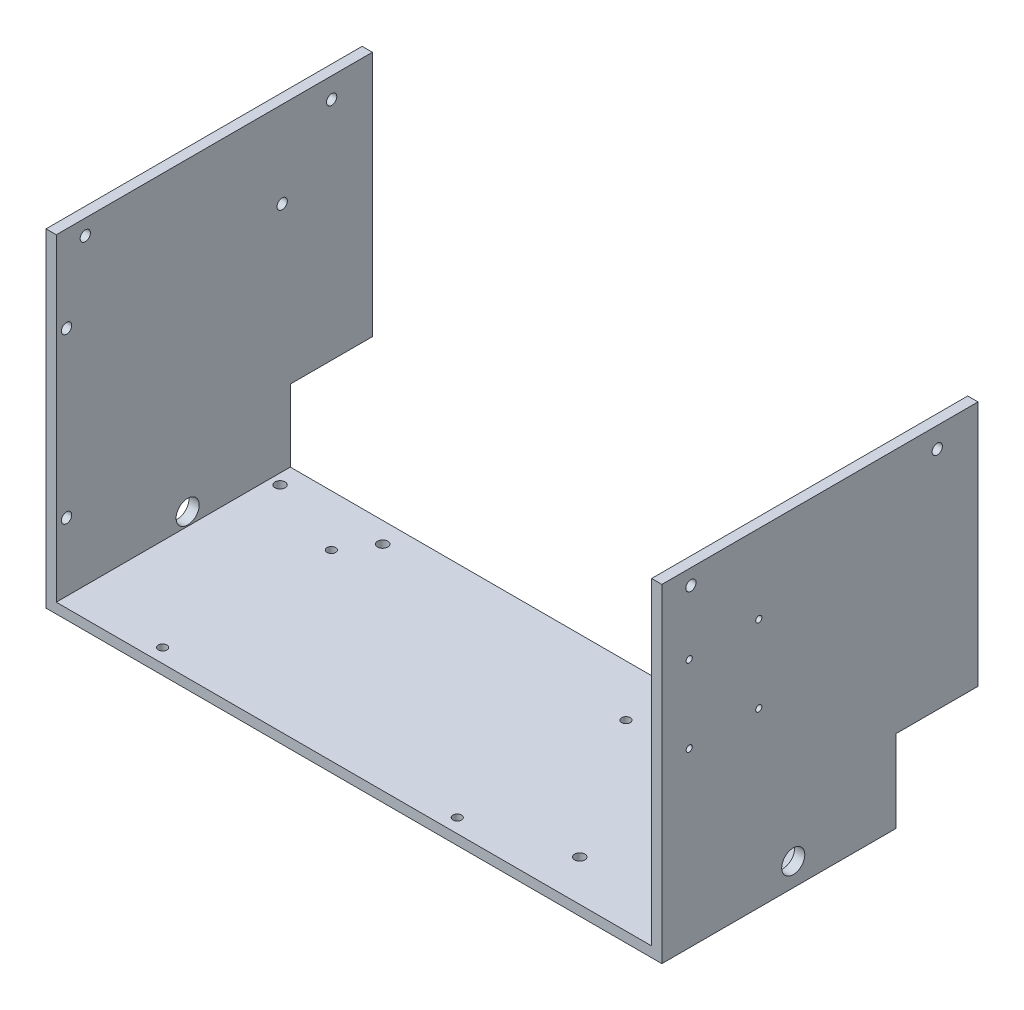
SolidWorks part; units mm, degrees
ref_plane "Front Plane" through (0, 0, 0) normal (0, 0, 1) x (1, 0, 0)
ref_plane "Top Plane" through (0, 0, 0) normal (0, 1, 0) x (1, 0, 0)
ref_plane "Right Plane" through (0, 0, 0) normal (1, 0, 0) x (0, 0, -1)
sketch "Sketch1" plane through (0, 0, 0) normal (0, 1, 0) x (1, 0, 0)
  line L1 (0, 0) -> (381, 0)
  line L2 (0, 0) -> (0, 429.26)
  line L3 (0, 429.26) -> (381, 429.26)
  line L4 (381, 0) -> (381, 429.26)
  dimension "D1" = 429.26
  dimension "D2" = 381
extrude "Boss-Extrude1" add sketch "Sketch1" along normal blind 6.35
sketch "Sketch2" plane through (0, 6.35, 0) normal (0, 1, 0) x (1, 0, 0)
  line L0 (0, 0) -> (381, 0) construction
  line L1 (63.5, 203.2) -> (317.5, 203.2)
  line L2 (63.5, 203.2) -> (63.5, 0)
  line L3 (63.5, 0) -> (317.5, 0)
  line L4 (317.5, 203.2) -> (317.5, 0)
  line L5 (381, 0) -> (381, 429.26) construction
  dimension "D1" = 254
  dimension "D2" = 203.2
  dimension "D3" = 0
  dimension "D4" = 63.5
extrude "Cut-Extrude1" cut sketch "Sketch2" against normal blind 6.35
sketch "Sketch3" plane through (0, 6.35, 0) normal (0, 1, 0) x (1, 0, 0)
  line L0 (381, 0) -> (381, 429.26) construction
  line L1 (0, 0) -> (381, 0)
  line L2 (0, 0) -> (0, 73.66)
  line L3 (0, 73.66) -> (381, 73.66)
  line L4 (381, 0) -> (381, 73.66)
  dimension "D1" = 73.66
extrude "Cut-Extrude2" cut sketch "Sketch3" against normal blind 6.35
sketch "Sketch4" plane through (0, 0, -203.2) normal (0, 0, 1) x (1, 0, 0)
  line L0 (317.5, 6.35) -> (63.5, 6.35) construction
  line L1 (63.5, 0) -> (317.5, 0)
  line L2 (63.5, 0) -> (63.5, 6.35)
  line L3 (63.5, 6.35) -> (317.5, 6.35)
  line L4 (317.5, 0) -> (317.5, 6.35)
  line L5 (63.5, 0) -> (63.5, 6.35) construction
  line L6 (317.5, 0) -> (63.5, 0) construction
  dimension "D1" = 254
  dimension "D2" = 0
  dimension "D3" = 0
extrude "Cut-Extrude3" cut sketch "Sketch4" against normal blind 73.66
sketch "Sketch6" plane through (0, 6.35, 0) normal (0, 1, 0) x (1, 0, 0)
  line L1 (381, 429.26) -> (374.65, 429.26)
  line L2 (381, 429.26) -> (381, 233.68)
  line L3 (381, 233.68) -> (374.65, 233.68)
  line L4 (374.65, 429.26) -> (374.65, 233.68)
  dimension "D1" = 6.35
  dimension "D2" = 195.58
extrude "Boss-Extrude2" add sketch "Sketch6" along normal blind 171.45
sketch "Sketch7" plane through (0, 6.35, 0) normal (0, 1, 0) x (1, 0, 0)
  line L1 (0, 429.26) -> (6.35, 429.26)
  line L2 (0, 429.26) -> (0, 233.68)
  line L3 (0, 233.68) -> (6.35, 233.68)
  line L4 (6.35, 429.26) -> (6.35, 233.68)
  dimension "D1" = 195.58
  dimension "D2" = 6.35
extrude "Boss-Extrude3" add sketch "Sketch7" along normal blind 158.75
sketch "Sketch8" plane through (0, 0, -429.26) normal (0, 0, -1) x (-1, 0, 0)
  line L1 (-6.35, 165.1) -> (0, 165.1)
  line L2 (-6.35, 165.1) -> (-6.35, 0)
  line L3 (-6.35, 0) -> (0, 0)
  line L4 (0, 165.1) -> (0, 0)
extrude "Boss-Extrude4" add sketch "Sketch8" along normal blind 50.8
sketch "Sketch9" plane through (0, 0, -233.68) normal (0, 0, 1) x (1, 0, 0)
  line L1 (6.35, 165.1) -> (0, 165.1)
  line L2 (6.35, 165.1) -> (6.35, 6.35)
  line L3 (6.35, 6.35) -> (0, 6.35)
  line L4 (0, 165.1) -> (0, 6.35)
extrude "Cut-Extrude4" cut sketch "Sketch9" against normal blind 50.8
sketch "Sketch10" plane through (0, 0, -429.26) normal (0, 0, -1) x (-1, 0, 0)
  line L0 (-381, 0) -> (-6.35, 0) construction
  line L1 (-381, 177.8) -> (-374.1001, 177.8)
  line L2 (-381, 177.8) -> (-381, 0)
  line L3 (-381, 0) -> (-374.1001, 0)
  line L4 (-374.1001, 177.8) -> (-374.1001, 0)
extrude "Boss-Extrude5" add sketch "Sketch10" along normal blind 50.8
sketch "Sketch11" plane through (0, 0, -233.68) normal (0, 0, 1) x (1, 0, 0)
  line L1 (381, 6.35) -> (374.65, 6.35)
  line L2 (381, 6.35) -> (381, 177.8)
  line L3 (381, 177.8) -> (374.65, 177.8)
  line L4 (374.65, 6.35) -> (374.65, 177.8)
extrude "Cut-Extrude5" cut sketch "Sketch11" against normal blind 50.8
sketch "Sketch13" plane through (0, 0, -429.26) normal (0, 0, 1) x (1, 0, 0)
  line L1 (374.65, 177.8) -> (374.1001, 177.8)
  line L2 (374.65, 177.8) -> (374.65, 6.35)
  line L3 (374.65, 6.35) -> (374.1001, 6.35)
  line L4 (374.1001, 177.8) -> (374.1001, 6.35)
extrude "Cut-Extrude6" cut sketch "Sketch13" against normal blind 50.8
sketch "Sketch14" plane through (0, 0, -480.06) normal (0, 0, -1) x (-1, 0, 0)
  line L1 (-381, 177.8) -> (-374.1001, 177.8)
  line L2 (-381, 177.8) -> (-381, 0)
  line L3 (-381, 0) -> (-374.1001, 0)
  line L4 (-374.1001, 177.8) -> (-374.1001, 0)
extrude "Cut-Extrude7" cut sketch "Sketch14" against normal blind 50.8
sketch "Sketch15" plane through (0, 0, -480.06) normal (0, 0, -1) x (-1, 0, 0)
  line L1 (-6.35, 165.1) -> (0, 165.1)
  line L2 (-6.35, 165.1) -> (-6.35, 0)
  line L3 (-6.35, 0) -> (0, 0)
  line L4 (0, 165.1) -> (0, 0)
extrude "Cut-Extrude8" cut sketch "Sketch15" against normal blind 50.8
sketch "Sketch16" plane through (0, 177.8, 0) normal (0, 1, 0) x (1, 0, 0)
  line L1 (381, 284.48) -> (374.65, 284.48)
  line L2 (381, 284.48) -> (381, 429.26)
  line L3 (381, 429.26) -> (374.65, 429.26)
  line L4 (374.65, 284.48) -> (374.65, 429.26)
extrude "Boss-Extrude6" add sketch "Sketch16" along normal blind 25.4
sketch "Sketch17" plane through (0, 165.1, 0) normal (0, 1, 0) x (1, 0, 0)
  line L1 (6.35, 284.48) -> (0, 284.48)
  line L2 (6.35, 284.48) -> (6.35, 429.26)
  line L3 (6.35, 429.26) -> (0, 429.26)
  line L4 (0, 284.48) -> (0, 429.26)
extrude "Boss-Extrude7" add sketch "Sketch17" against normal blind 19.05
sketch "Sketch19" plane through (0, 0, -429.26) normal (0, 0, -1) x (-1, 0, 0)
  line L0 (0, 0) -> (0, 165.1) construction
  line L1 (-6.35, 190.5) -> (0, 190.5)
  line L2 (-6.35, 190.5) -> (-6.35, 50.8)
  line L3 (-6.35, 50.8) -> (0, 50.8)
  line L4 (0, 190.5) -> (0, 50.8)
  dimension "D1" = 139.7
extrude "Boss-Extrude8" add sketch "Sketch19" along normal blind 50.8
sketch "Sketch20" plane through (0, 190.5, 0) normal (0, 1, 0) x (1, 0, 0)
  line L1 (6.35, 284.48) -> (0, 284.48)
  line L2 (6.35, 284.48) -> (6.35, 480.06)
  line L3 (6.35, 480.06) -> (0, 480.06)
  line L4 (0, 284.48) -> (0, 480.06)
extrude "Boss-Extrude9" add sketch "Sketch20" against normal blind 31.75
sketch "Sketch21" plane through (0, 0, -429.26) normal (0, 0, -1) x (-1, 0, 0)
  line L0 (-374.65, 6.35) -> (-374.65, 203.2) construction
  line L1 (-381, 203.2) -> (-374.65, 203.2)
  line L2 (-381, 203.2) -> (-381, 63.5)
  line L3 (-381, 63.5) -> (-374.65, 63.5)
  line L4 (-374.65, 203.2) -> (-374.65, 63.5)
  dimension "D1" = 139.7
extrude "Boss-Extrude10" add sketch "Sketch21" along normal blind 50.8
sketch "Sketch22" plane through (0, 203.2, 0) normal (0, 1, 0) x (1, 0, 0)
  line L0 (374.65, 480.06) -> (374.65, 284.48) construction
  line L1 (381, 284.48) -> (374.65, 284.48)
  line L2 (381, 284.48) -> (381, 480.06)
  line L3 (381, 480.06) -> (374.65, 480.06)
  line L4 (374.65, 284.48) -> (374.65, 480.06)
extrude "Boss-Extrude11" add sketch "Sketch22" against normal blind 50.8
sketch "Sketch23" plane through (0, 63.5, 0) normal (0, -1, 0) x (1, 0, 0)
  line L1 (381, -480.06) -> (374.65, -480.06)
  line L2 (381, -480.06) -> (381, -429.26)
  line L3 (381, -429.26) -> (374.65, -429.26)
  line L4 (374.65, -480.06) -> (374.65, -429.26)
extrude "Boss-Extrude12" add sketch "Sketch23" along normal blind 12.7
sketch "Sketch24" plane through (0, 190.5, 0) normal (0, 1, 0) x (1, 0, 0)
  line L0 (0, 480.06) -> (6.35, 480.06) construction
  line L1 (6.35, 284.48) -> (0, 284.48)
  line L2 (6.35, 284.48) -> (6.35, 480.06)
  line L3 (6.35, 480.06) -> (0, 480.06)
  line L4 (0, 284.48) -> (0, 480.06)
extrude "Boss-Extrude13" add sketch "Sketch24" along normal blind 12.7
sketch "Sketch26" plane through (0, 6.35, 0) normal (0, 1, 0) x (1, 0, 0)
  line L1 (0, 73.66) -> (381, 73.66)
  line L2 (0, 73.66) -> (0, 284.48)
  line L3 (0, 284.48) -> (381, 284.48)
  line L4 (381, 73.66) -> (381, 284.48)
extrude "Cut-Extrude9" cut sketch "Sketch26" against normal blind 12.7
sketch "Sketch27" plane through (0, 0, 0) normal (-1, 0, 0) x (0, 0, 1)
  line L0 (-284.48, 6.35) -> (-429.26, 6.35) construction
  circle A0 centre (-365.76, 14.224) radius 7.1438
  dimension "D1" = 7.874
  dimension "D2" = 14.2875
extrude "Cut-Extrude12" cut sketch "Sketch27" against normal blind 8.89
sketch "Sketch29" plane through (381, 0, 0) normal (1, 0, 0) x (0, 0, -1)
  line L0 (429.26, 50.8) -> (429.26, 0) construction
  line L1 (284.48, 0) -> (429.26, 0) construction
  circle A0 centre (365.76, 14.224) radius 7.1437
  dimension "D1" = 14.2875
  dimension "D2" = 63.5
  dimension "D3" = 14.2875
  dimension "D4" = 14.224
extrude "Cut-Extrude13" cut sketch "Sketch29" against normal blind 8.89
sketch "Sketch31" plane through (0, 6.35, 0) normal (0, 1, 0) x (1, 0, 0)
  line L0 (374.65, 429.26) -> (6.35, 429.26) construction
  line L1 (381, 284.48) -> (381, 429.26) construction
  line L2 (0, 480.06) -> (0, 284.48) construction
  circle A0 centre (368.3, 416.56) radius 3.175
  circle A1 centre (304.8, 416.56) radius 3.175
  circle A2 centre (12.7, 416.56) radius 3.175
  circle A3 centre (76.2, 416.56) radius 3.175
  dimension "D1" = 6.35
  dimension "D2" = 12.7
  dimension "D3" = 12.7
  dimension "D4" = 6.35
  dimension "D5" = 12.7
  dimension "D6" = 76.2
  dimension "D7" = 6.35
  dimension "D8" = 12.7
  dimension "D9" = 12.7
  dimension "D10" = 12.7
  dimension "D11" = 6.35
  dimension "D12" = 76.2
extrude "Cut-Extrude14" cut sketch "Sketch31" against normal blind 12.7
sketch "Sketch36" plane through (381, 0, 0) normal (1, 0, 0) x (0, 0, -1)
  line L0 (284.48, 203.2) -> (480.06, 203.2) construction
  line L1 (284.48, 0) -> (284.48, 203.2) construction
  circle A0 centre (344.4513, 154.5488) radius 1.905
  circle A1 centre (301.3983, 154.5512) radius 1.905
  circle A2 centre (344.4513, 106.7992) radius 1.905
  circle A3 centre (301.3983, 106.7992) radius 1.905
  dimension "D1" = 3.81
  dimension "D2" = 48.6512
  dimension "D3" = 59.9713
  dimension "D4" = 16.9183
  dimension "D5" = 48.6488
  dimension "D6" = 16.9183
  dimension "D7" = 3.81
  dimension "D8" = 3.81
  dimension "D9" = 3.81
  dimension "D10" = 96.4008
  dimension "D11" = 59.9713
  dimension "D12" = 96.4008
extrude "Cut-Extrude17" cut sketch "Sketch36" against normal blind 12.7
sketch "Sketch37" plane through (0, 6.35, 0) normal (0, 1, 0) x (1, 0, 0)
  line L0 (0, 429.26) -> (0, 284.48) construction
  line L1 (6.35, 284.48) -> (6.35, 429.26) construction
  line L2 (374.65, 429.26) -> (6.35, 429.26) construction
  line L3 (374.65, 284.48) -> (6.35, 284.48) construction
  circle A0 centre (63.5, 397.51) radius 2.667
  circle A1 centre (63.5, 293.116) radius 2.667
  circle A2 centre (245.7704, 293.116) radius 2.667
  circle A3 centre (245.7704, 397.51) radius 2.667
  dimension "D1" = 5.334
  dimension "D2" = 63.5
  dimension "D3" = 5.334
  dimension "D4" = 63.5
  dimension "D5" = 57.15
  dimension "D6" = 104.394
  dimension "D7" = 31.75
  dimension "D8" = 5.334
  dimension "D9" = 182.2704
  dimension "D10" = 104.394
  dimension "D11" = 8.636
  dimension "D12" = 5.334
  dimension "D13" = 31.75
  dimension "D14" = 182.2704
  dimension "D15" = 8.636
extrude "Cut-Extrude18" cut sketch "Sketch37" against normal blind 17.78
sketch "Sketch38" plane through (0, 6.35, 0) normal (0, 1, 0) x (1, 0, 0)
  line L0 (381, 284.48) -> (381, 480.06) construction
  line L1 (374.65, 284.48) -> (6.35, 284.48) construction
  line L2 (374.65, 429.26) -> (374.65, 284.48) construction
  line L3 (292.1, 403.86) -> (292.1, 264.16) construction
  circle A0 centre (304.8, 309.88) radius 3.175
  circle A1 centre (361.95, 337.82) radius 3.175
  dimension "D1" = 6.35
  dimension "D2" = 76.2
  dimension "D3" = 25.4
  dimension "D4" = 6.35
  dimension "D5" = 27.94
  dimension "D6" = 57.15
  dimension "D7" = 12.7
  dimension "D8" = 12.7
  dimension "D9" = 12.7
extrude "Cut-Extrude19" cut sketch "Sketch38" against normal blind 17.78
sketch "Sketch39" plane through (0, 0, 0) normal (-1, 0, 0) x (0, 0, 1)
  line L0 (-480.06, 203.2) -> (-284.48, 203.2) construction
  circle A0 centre (-454.8438, 190.5) radius 3.175
  circle A1 centre (-302.4438, 193.675) radius 3.175
  dimension "D1" = 12.7
  dimension "D2" = 6.35
  dimension "D3" = 6.35
extrude "Cut-Extrude20" cut sketch "Sketch39" against normal blind 17.78
sketch "Sketch41" plane through (0, 0, 0) normal (-1, 0, 0) x (0, 0, 1)
  line L0 (-284.48, 203.2) -> (-284.48, 0) construction
  line L1 (-480.06, 203.2) -> (-284.48, 203.2) construction
  circle A0 centre (-424.2308, 149.9108) radius 3.175
  circle A2 centre (-290.8808, 48.387) radius 3.175
  circle A3 centre (-290.8808, 149.9108) radius 3.175
  dimension "D1" = 6.35
  dimension "D2" = 139.7508
  dimension "D3" = 53.2892
  dimension "D7" = 6.35
  dimension "D8" = 6.4008
  dimension "D9" = 154.813
  dimension "D10" = 6.35
  dimension "D11" = 6.4008
  dimension "D12" = 53.2892
extrude "Cut-Extrude21" cut sketch "Sketch41" against normal blind 15.24
sketch "Sketch42" plane through (381, 0, 0) normal (1, 0, 0) x (0, 0, -1)
  circle A0 centre (454.8438, 190.5) radius 3.302
  circle A1 centre (302.4438, 193.675) radius 3.302
  dimension "D1" = 6.604
  dimension "D2" = 6.604
extrude "Cut-Extrude22" cut sketch "Sketch42" against normal blind 12.7
sketch "Sketch43" plane through (381, 0, 0) normal (1, 0, 0) x (0, 0, -1)
  circle A0 centre (302.4438, 193.675) radius 3.175
  circle A1 centre (302.4438, 193.675) radius 3.302
  circle A2 centre (454.8438, 190.5) radius 3.175
  circle A3 centre (454.8438, 190.5) radius 3.302
  dimension "D1" = 6.35
  dimension "D2" = 6.604
  dimension "D3" = 6.35
  dimension "D4" = 6.604
extrude "Boss-Extrude14" add sketch "Sketch43" against normal blind 6.35
